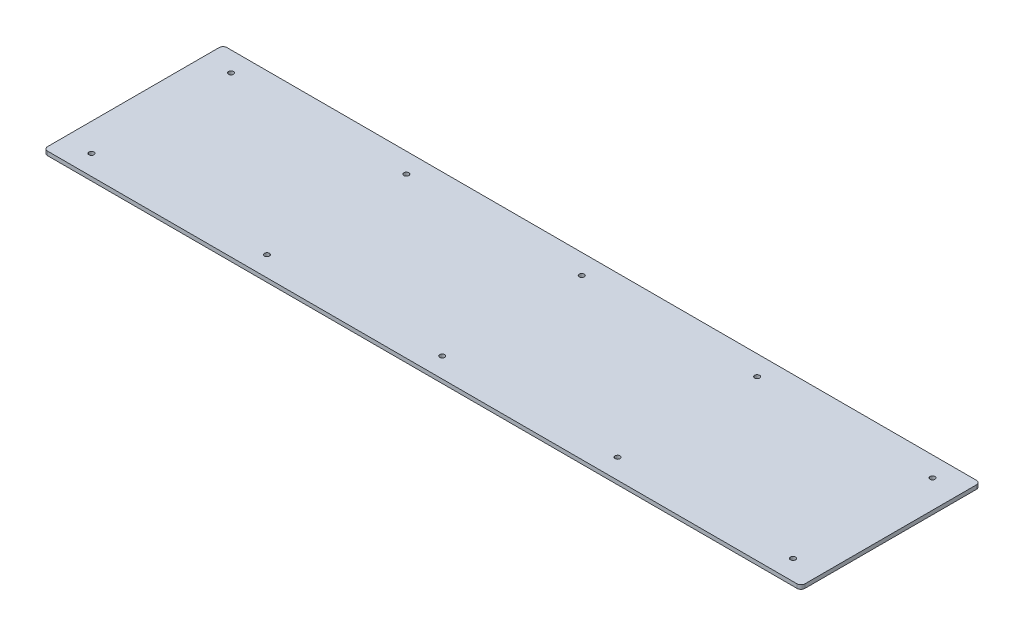
SolidWorks part; units mm, degrees
ref_plane "Front Plane" through (0, 0, 0) normal (0, 0, 1) x (1, 0, 0)
ref_plane "Top Plane" through (0, 0, 0) normal (0, 1, 0) x (1, 0, 0)
ref_plane "Right Plane" through (0, 0, 0) normal (1, 0, 0) x (0, 0, -1)
sketch "Sketch1" plane through (0, 0, 0) normal (0, 1, 0) x (1, 0, 0)
  line L1 (0, 0) -> (1206.5, 0)
  line L2 (0, 0) -> (0, 285.75)
  line L3 (0, 285.75) -> (1206.5, 285.75)
  line L4 (1206.5, 0) -> (1206.5, 285.75)
  dimension "D1" = 285.75
  dimension "D2" = 1206.5
extrude "Boss-Extrude1" add sketch "Sketch1" along normal blind 6.35
hole_wizard "5/16 (0.3125) Diameter Hole1" positions "Sketch2" profile "Sketch3" hole size "5/16" standard "ANSI Inch" end condition through all
sketch "Sketch2" plane through (0, 6.35, 0) normal (0, 1, 0) x (1, 0, 0)
  line L0 (0, 0) -> (1206.5, 0) construction
  line L1 (0, 285.75) -> (0, 0) construction
  point P0 (44.45, 31.75)
  dimension "D1" = 31.75
  dimension "D2" = 44.45
sketch "Sketch3" plane through (44.45, 6.35, -31.75) normal (1, 0, 0) x (0, 0, 1)
  line L0 (0, 0) -> (0, 6.35)
  line L1 (0, 6.35) -> (3.9687, 6.35)
  line L2 (3.9687, 6.35) -> (3.9687, 0)
  line L5 (3.9687, 0) -> (0, 0)
  line L11 (0, -6.35) -> (0, 107.95) construction
  dimension "Thru Hole Dia." = 7.9375
  dimension "Thru Hole Depth" = 6.35
pattern_linear "LPattern1" count 5 spacing 279.4 along (1, 0, 0) count 2 spacing 222.25 along (0, 0, -1) of "5/16 (0.3125) Diameter Hole1"
fillet "Fillet1" radius 6.35 4 edges at (1206.5, 3.175, -285.75) (1206.5, 3.175, 0) (0, 3.175, 0) (0, 3.175, -285.75)
